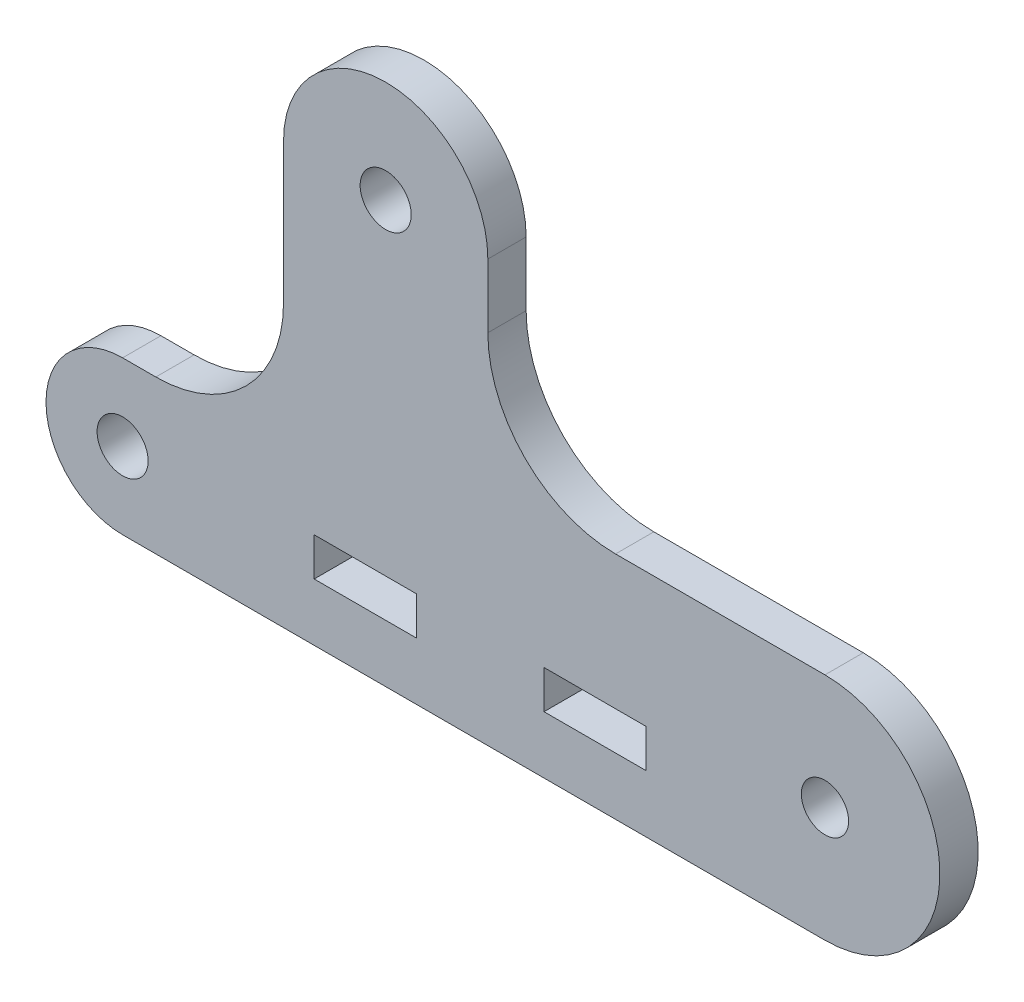
SolidWorks part; units mm, degrees
ref_plane "Front Plane" through (0, 0, 0) normal (0, 0, 1) x (1, 0, 0)
ref_plane "Top Plane" through (0, 0, 0) normal (0, 1, 0) x (1, 0, 0)
ref_plane "Right Plane" through (0, 0, 0) normal (1, 0, 0) x (0, 0, -1)
sketch "Sketch1" plane through (0, 0, 0) normal (0, 0, 1) x (1, 0, 0)
  line L0 (-27.5, 0) -> (27.5, 0)
  line L1 (-27.5, 6) -> (-12.5, 6) construction
  line L2 (-14.9, 33) -> (-14.9, 22)
  line L3 (-12.5, 7.5) -> (-4.5, 7.5)
  line L4 (-12.5, 7.5) -> (-12.5, 4.5)
  line L5 (-12.5, 4.5) -> (-4.5, 4.5)
  line L6 (-4.5, 7.5) -> (-4.5, 4.5)
  line L7 (5.5, 7.5) -> (13.5, 7.5)
  line L8 (5.5, 7.5) -> (5.5, 4.5)
  line L9 (5.5, 4.5) -> (13.5, 4.5)
  line L10 (13.5, 7.5) -> (13.5, 4.5)
  line L11 (-24.9, 12) -> (-27.5, 12)
  line L12 (1.1, 33) -> (1.1, 28)
  line L13 (11.1, 18) -> (27.5, 18)
  arc A0 (-27.5, 0) -> (-27.5, 12) centre (-27.5, 6) cw
  arc A1 (27.5, 0) -> (27.5, 18) centre (27.5, 9) ccw
  circle A2 centre (-27.5, 6) radius 2
  circle A3 centre (27.5, 9) radius 1.85
  circle A4 centre (-6.9, 33) radius 2
  circle A5 centre (-6.9, 33) radius 8 construction
  arc A6 (1.1, 28) -> (11.1, 18) centre (11.1, 28) ccw
  arc A7 (-14.9, 22) -> (-24.9, 12) centre (-24.9, 22) cw
  arc A8 (-14.9, 33) -> (1.1, 33) centre (-6.9, 33) cw
  dimension "D2" = 9
  dimension "D3" = 6
  dimension "D4" = 4
  dimension "D5" = 3.7
  dimension "D8" = 16
  dimension "D13" = 10
  dimension "D1" = 55
  dimension "D6" = 33
  dimension "D7" = 6.9
  dimension "D9" = 15
  dimension "D10" = 8
  dimension "D11" = 3
  dimension "D12" = 10
extrude "Boss-Extrude1" add sketch "Sketch1" along normal mid plane 3
